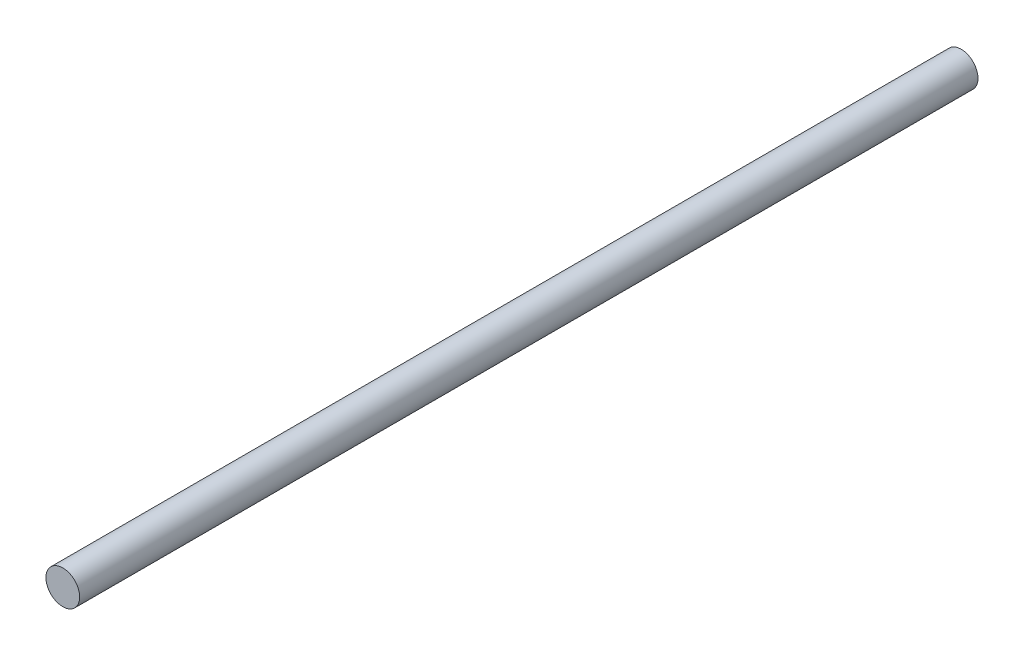
SolidWorks part; units mm, degrees
ref_plane "前基準面" through (0, 0, 0) normal (0, 0, 1) x (1, 0, 0)
ref_plane "上基準面" through (0, 0, 0) normal (0, 1, 0) x (1, 0, 0)
ref_plane "右基準面" through (0, 0, 0) normal (1, 0, 0) x (0, 0, -1)
sketch "草圖1" plane through (0, 0, 0) normal (0, 0, 1) x (1, 0, 0)
  circle A0 centre (0, 0) radius 15
  dimension "D1" = 30
extrude "填料-伸長1" add sketch "草圖1" along normal blind 800
